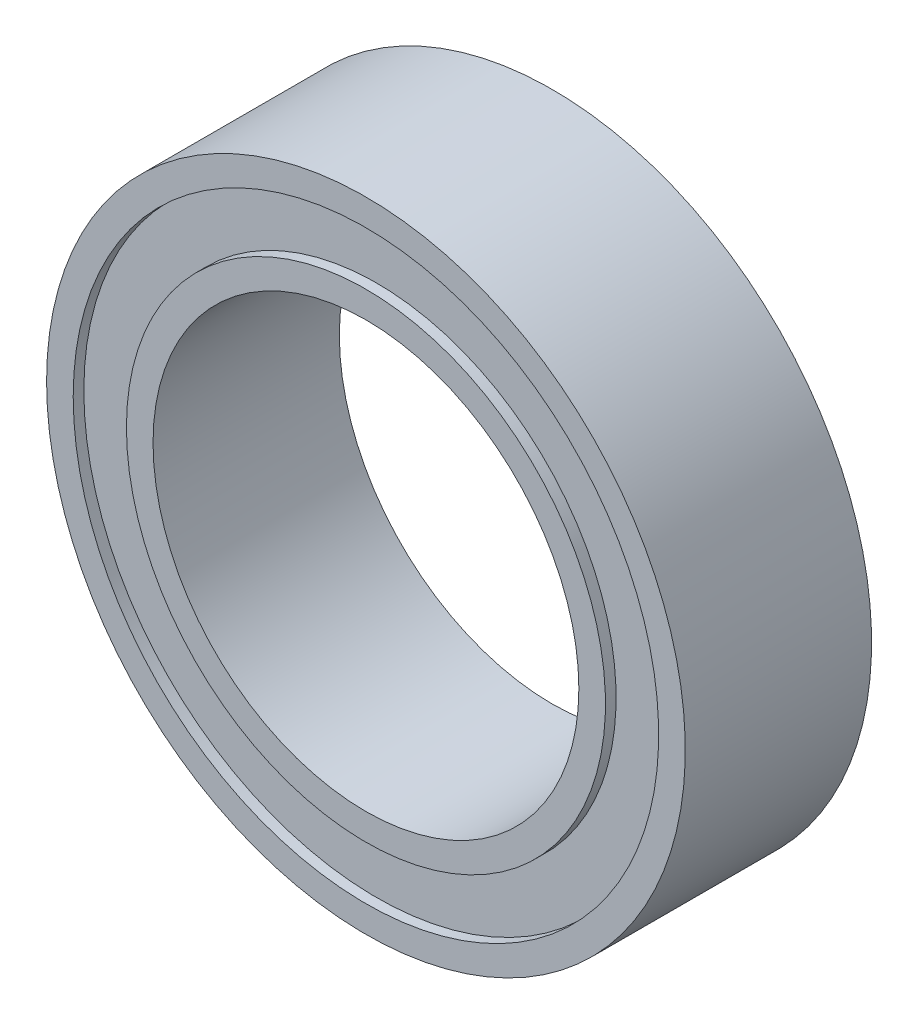
SolidWorks part; units mm, degrees
ref_plane "Front plane" through (0, 0, 0) normal (0, 0, 1) x (1, 0, 0)
ref_plane "Top plane" through (0, 0, 0) normal (0, 1, 0) x (1, 0, 0)
ref_plane "Right Plane" through (0, 0, 0) normal (1, 0, 0) x (0, 0, -1)
sketch "Sketch1" plane through (0, 0, 0) normal (0, 1, 0) x (1, 0, 0)
  line L0 (0, 1.75) -> (0, -1.75) construction
  line L1 (5.5, 1.75) -> (6, 1.75)
  line L2 (4, 1.75) -> (4.5, 1.75)
  line L3 (4, 1.75) -> (4, -1.75)
  line L4 (4, -1.75) -> (4.5, -1.75)
  line L5 (6, 1.75) -> (6, -1.75)
  line L7 (4.5, 1.75) -> (4.5, 1.55)
  line L8 (4.5, 1.55) -> (5.5, 1.55)
  line L9 (5.5, 1.75) -> (5.5, 1.55)
  line L11 (5.5, -1.75) -> (5.5, -1.55)
  line L12 (5.5, -1.55) -> (4.5, -1.55)
  line L13 (4.5, -1.75) -> (4.5, -1.55)
  line L14 (5.5, -1.75) -> (6, -1.75)
  dimension "D1" = 8
  dimension "D2" = 3.5
  dimension "D3" = 12
  dimension "D4" = 0.5
  dimension "D5" = 0.2
revolve "Revolve1" add sketch "Sketch1" angle 360 about L0
